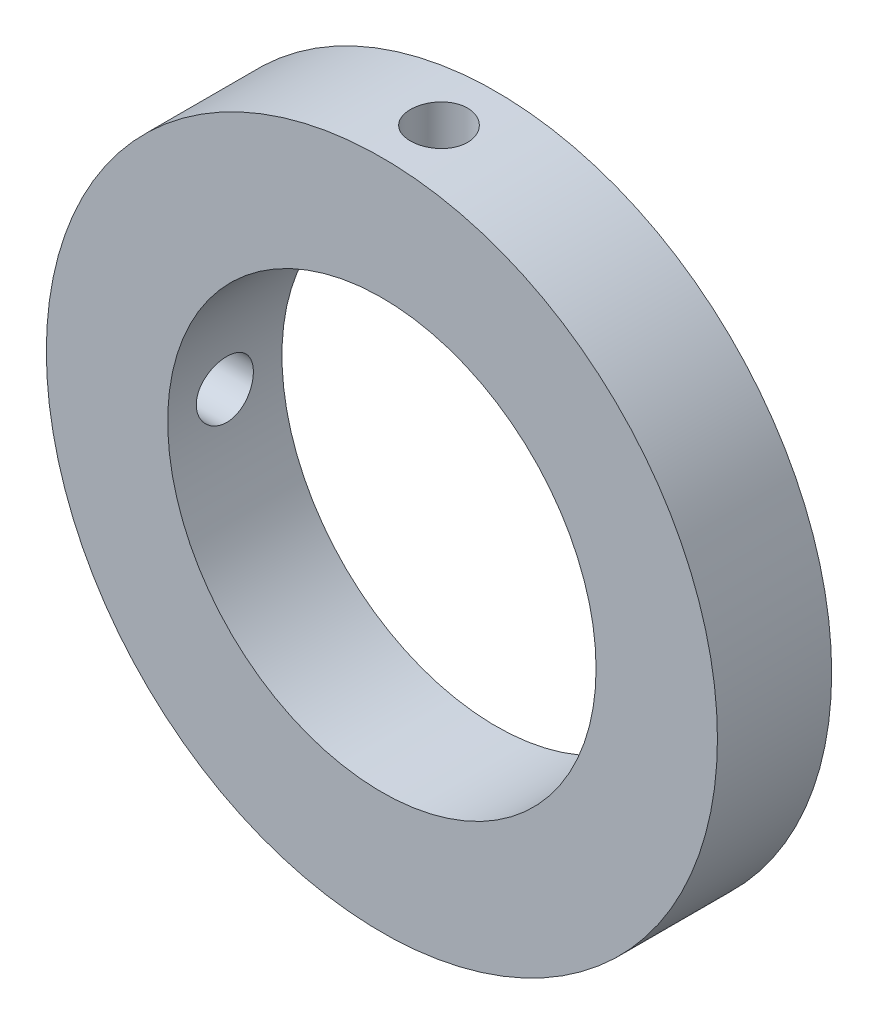
SolidWorks part; units mm, degrees
material "6063-O, Extruded Rod (SS)"
ref_plane "Front Plane" through (0, 0, 0) normal (0, 0, 1) x (1, 0, 0)
ref_plane "Top Plane" through (0, 0, 0) normal (0, 1, 0) x (1, 0, 0)
ref_plane "Right Plane" through (0, 0, 0) normal (1, 0, 0) x (0, 0, -1)
sketch "Sketch1" plane through (0, 0, 0) normal (0, 0, 1) x (1, 0, 0)
  circle A0 centre (0, 0) radius 15
  circle A1 centre (0, 0) radius 23.5
  dimension "D1" = 30
  dimension "D2" = 47
extrude "Boss-Extrude1" add sketch "Sketch1" along normal blind 8
sketch "Sketch2" plane through (0, 0, 8) normal (0, 0, 1) x (1, 0, 0)
  line L0 (0, 0) -> (0, 23.5) construction
  circle A0 centre (0, 0) radius 23.5 construction
ref_plane "Plane1" through (0, 23.5, 8) normal (0, 1, 0) x (1, 0, 0)
sketch "Sketch3" plane through (0, 23.5, 8) normal (0, 1, 0) x (1, 0, 0)
  line L0 (0, 0) -> (0, 8) construction
  line L1 (-23.5, 0) -> (23.5, 0) construction
  circle A0 centre (0, 4) radius 2
  dimension "D1" = 4
extrude "Cut-Extrude1" cut sketch "Sketch3" against normal up to surface (8.5 mm away)
pattern_circular "CirPattern1" count 2 every 90 about axis through (0, 0, 8) along (0, 0, 1) of "Cut-Extrude1"
